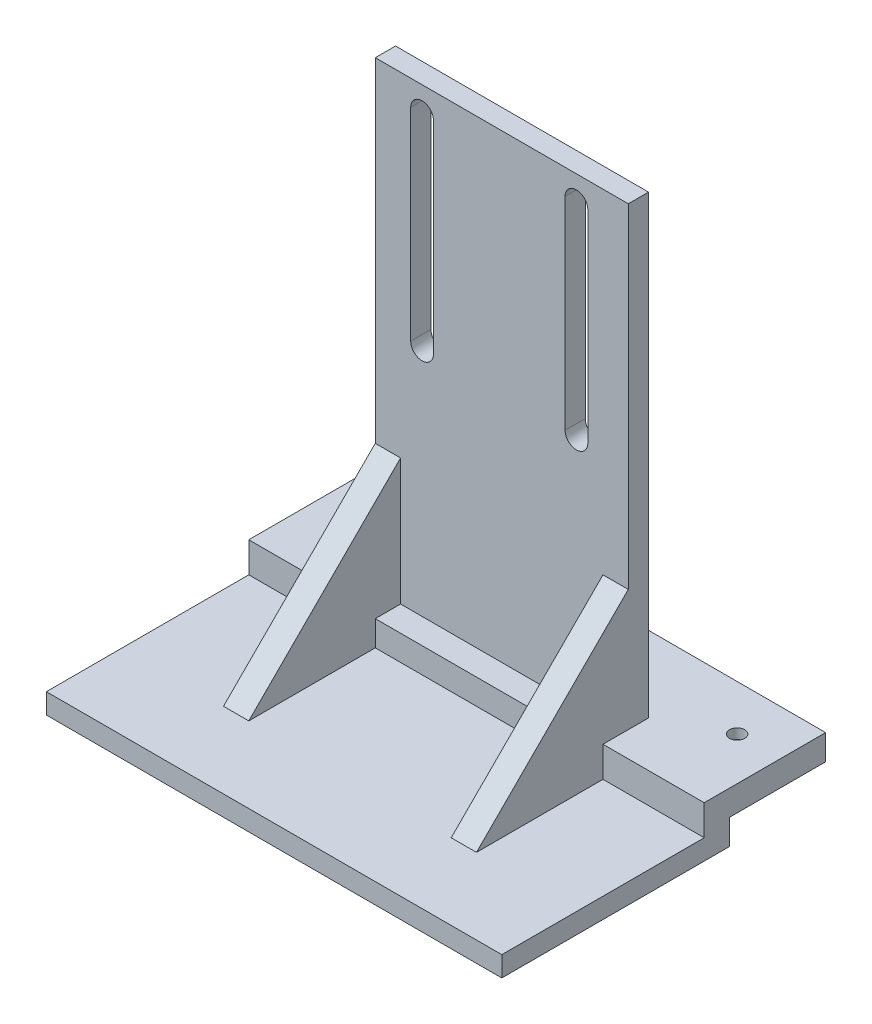
SolidWorks part; units mm, degrees
ref_plane "Plan de face" through (0, 0, 0) normal (0, 0, 1) x (1, 0, 0)
ref_plane "Plan de dessus" through (0, 0, 0) normal (0, 1, 0) x (1, 0, 0)
ref_plane "Plan de droite" through (0, 0, 0) normal (1, 0, 0) x (0, 0, -1)
sketch "Esquisse1" plane through (0, 0, 0) normal (0, 0, 1) x (1, 0, 0)
  line L0 (-29.394, -11.0728) -> (20.606, -11.0728) construction
  line L1 (-29.394, 33.9272) -> (20.606, 33.9272)
  line L2 (-29.394, 33.9272) -> (-29.394, -61.0728)
  line L3 (-29.394, -61.0728) -> (20.606, -61.0728)
  line L4 (20.606, 33.9272) -> (20.606, -61.0728)
  dimension "D1" = 50
  dimension "D2" = 95
  dimension "D3" = 45
extrude "Boss.-Extru.1" add sketch "Esquisse1" along normal blind 4
sketch "Esquisse2" plane through (0, 0, 4) normal (0, 0, 1) x (1, 0, 0)
  line L0 (20.606, -61.0728) -> (20.606, 33.9272) construction
  line L1 (-29.394, -61.0728) -> (20.606, -61.0728)
  line L2 (-29.394, -61.0728) -> (-29.394, -57.0728)
  line L3 (-29.394, -57.0728) -> (20.606, -57.0728)
  line L4 (20.606, -61.0728) -> (20.606, -57.0728)
  dimension "D1" = 4
extrude "Boss.-Extru.2" add sketch "Esquisse2" along normal blind 5
sketch "Esquisse3" plane through (0, -61.0728, 0) normal (0, -1, 0) x (1, 0, 0)
  line L0 (-29.394, 9) -> (-29.394, 0) construction
  line L1 (20.606, 9) -> (-29.394, 9)
  line L2 (20.606, 9) -> (20.606, 4)
  line L3 (20.606, 4) -> (-29.394, 4)
  line L4 (-29.394, 9) -> (-29.394, 4)
  dimension "D1" = 5
extrude "Boss.-Extru.3" add sketch "Esquisse3" along normal blind 5
sketch "Esquisse4" plane through (0, 0, 9) normal (0, 0, 1) x (1, 0, 0)
  line L0 (20.606, -66.0728) -> (20.606, -57.0728) construction
  line L1 (-29.394, -66.0728) -> (20.606, -66.0728)
  line L2 (-29.394, -66.0728) -> (-29.394, -62.0728)
  line L3 (-29.394, -62.0728) -> (20.606, -62.0728)
  line L4 (20.606, -66.0728) -> (20.606, -62.0728)
  dimension "D1" = 4
extrude "Boss.-Extru.4" add sketch "Esquisse4" along normal blind 40
sketch "Esquisse5" plane through (0, 0, 0) normal (0, 0, -1) x (-1, 0, 0)
  line L0 (29.394, 33.9272) -> (29.394, -61.0728) construction
  line L1 (-20.606, -61.0728) -> (29.394, -61.0728)
  line L2 (-20.606, -61.0728) -> (-20.606, -56.0728)
  line L3 (-20.606, -56.0728) -> (29.394, -56.0728)
  line L4 (29.394, -61.0728) -> (29.394, -56.0728)
  dimension "D1" = 5
extrude "Boss.-Extru.5" add sketch "Esquisse5" along normal blind 15
sketch "Esquisse6" plane through (0, 0, 4) normal (0, 0, 1) x (1, 0, 0)
  line L0 (-20.144, 28.9272) -> (-20.144, -11.0728) construction
  line L1 (-17.894, 28.9272) -> (-17.894, -11.0728)
  line L2 (-22.394, 28.9272) -> (-22.394, -11.0728)
  line L3 (10.356, 28.9272) -> (10.356, -11.0728) construction
  line L4 (12.606, 28.9272) -> (12.606, -11.0728)
  line L5 (8.106, 28.9272) -> (8.106, -11.0728)
  line L6 (-29.394, 33.9272) -> (-29.394, -57.0728) construction
  line L7 (20.606, 33.9272) -> (-29.394, 33.9272) construction
  arc A0 (-17.894, 28.9272) -> (-22.394, 28.9272) centre (-20.144, 28.9272) ccw
  arc A1 (-22.394, -11.0728) -> (-17.894, -11.0728) centre (-20.144, -11.0728) ccw
  arc A2 (12.606, 28.9272) -> (8.106, 28.9272) centre (10.356, 28.9272) ccw
  arc A3 (8.106, -11.0728) -> (12.606, -11.0728) centre (10.356, -11.0728) ccw
  point P2 (-20.144, 8.9272)
  point P7 (10.356, 8.9272)
  dimension "D1" = 7
  dimension "D2" = 4.5
  dimension "D3" = 26
  dimension "D4" = 4.5
  dimension "D5" = 5
  dimension "D6" = 5
  dimension "D7" = 45
  dimension "D8" = 45
extrude "Enlèv. mat.-Extru.1" cut sketch "Esquisse6" against normal up to next
sketch "Esquisse7" plane through (-29.394, 0, 0) normal (-1, 0, 0) x (0, 0, 1)
  line L0 (4, -32.0728) -> (34, -62.0728)
  line L1 (4, 33.9272) -> (4, -57.0728) construction
  line L2 (49, -62.0728) -> (9, -62.0728) construction
  line L3 (34, -62.0728) -> (4, -62.0728)
  line L4 (4, -66.0728) -> (4, -61.0728) construction
  line L5 (4, -62.0728) -> (4, -32.0728)
  dimension "D1" = 30
  dimension "D2" = 30
extrude "Boss.-Extru.6" add sketch "Esquisse7" against normal blind 5
sketch "Esquisse8" plane through (20.606, 0, 0) normal (1, 0, 0) x (0, 0, -1)
  line L0 (-4, -32.0728) -> (-34, -62.0728)
  line L1 (-4, -57.0728) -> (-4, 33.9272) construction
  line L2 (-4, -32.0728) -> (-4, -57.0728) construction
  line L3 (-49, -62.0728) -> (-9, -62.0728) construction
  line L4 (-34, -62.0728) -> (-4, -62.0728)
  line L5 (-4, -66.0728) -> (-4, -61.0728) construction
  line L6 (-4, -62.0728) -> (-4, -32.0728)
  dimension "D1" = 30
  dimension "D2" = 30
extrude "Boss.-Extru.7" add sketch "Esquisse8" against normal blind 5
sketch "Esquisse10" plane through (20.606, 0, 0) normal (1, 0, 0) x (0, 0, -1)
  line L0 (-49, -62.0728) -> (-49, -66.0728)
  line L1 (-49, -66.0728) -> (-4, -66.0728)
  line L2 (-4, -66.0728) -> (-4, -61.0728)
  line L3 (-4, -61.0728) -> (15, -61.0728)
  line L4 (15, -61.0728) -> (15, -56.0728)
  line L5 (15, -56.0728) -> (0, -56.0728)
  line L6 (0, -56.0728) -> (-9, -56.0728)
  line L7 (-9, -56.0728) -> (-9, -62.0728)
  line L8 (-9, -62.0728) -> (-49, -62.0728)
  dimension "D1" = 15
  dimension "D2" = 9
extrude "Boss.-Extru.8" add sketch "Esquisse10" along normal blind 20
sketch "Esquisse11" plane through (-29.394, 0, 0) normal (-1, 0, 0) x (0, 0, 1)
  line L0 (49, -66.0728) -> (4, -66.0728)
  line L1 (4, -66.0728) -> (4, -61.0728)
  line L2 (4, -61.0728) -> (-15, -61.0728)
  line L3 (-15, -61.0728) -> (-15, -56.0728)
  line L4 (-15, -56.0728) -> (0, -56.0728)
  line L5 (0, -56.0728) -> (9, -56.0728)
  line L6 (9, -56.0728) -> (9, -62.0728)
  line L7 (9, -62.0728) -> (49, -62.0728)
  line L19 (-15, -61.0728) -> (4, -61.0728)
  line L20 (4, -61.0728) -> (4, -66.0728)
  line L21 (4, -66.0728) -> (49, -66.0728)
  line L22 (49, -66.0728) -> (49, -62.0728)
  line L23 (49, -62.0728) -> (34, -62.0728)
  line L24 (34, -62.0728) -> (4, -32.0728)
  line L25 (4, -32.0728) -> (4, 33.9272)
  line L26 (4, 33.9272) -> (0, 33.9272)
  line L27 (0, 33.9272) -> (0, -56.0728)
  line L28 (0, -56.0728) -> (-15, -56.0728)
  line L29 (-15, -56.0728) -> (-15, -61.0728)
  line L33 (49, -66.0728) -> (49, -62.0728)
  point P4 (0, 0)
  point P17 (9, -61.0728)
  point P18 (9, -62.0728)
  dimension "D1" = 9
  dimension "D2" = 0
extrude "Boss.-Extru.9" add sketch "Esquisse11" along normal blind 20
sketch "Esquisse12" plane through (0, -56.0728, 0) normal (0, 1, 0) x (1, 0, 0)
  line L0 (15.606, -4) -> (-24.394, -4) construction
  line L1 (-49.394, -9) -> (-49.394, 15) construction
  circle A0 centre (32.106, 6) radius 1.5
  circle A1 centre (-40.894, 6) radius 1.5
  dimension "D1" = 3
  dimension "D2" = 3
  dimension "D3" = 10
  dimension "D4" = 10
  dimension "D5" = 73
  dimension "D6" = 8.5
extrude "Enlèv. mat.-Extru.2" cut sketch "Esquisse12" against normal up to next
sketch "Esquisse13" plane through (0, -61.0728, 0) normal (0, -1, 0) x (1, 0, 0)
  circle A0 centre (32.106, -6) radius 2
  circle A1 centre (-40.894, -6) radius 2
  dimension "D1" = 4
  dimension "D2" = 4
extrude "Enlèv. mat.-Extru.3" cut sketch "Esquisse13" against normal blind 3
